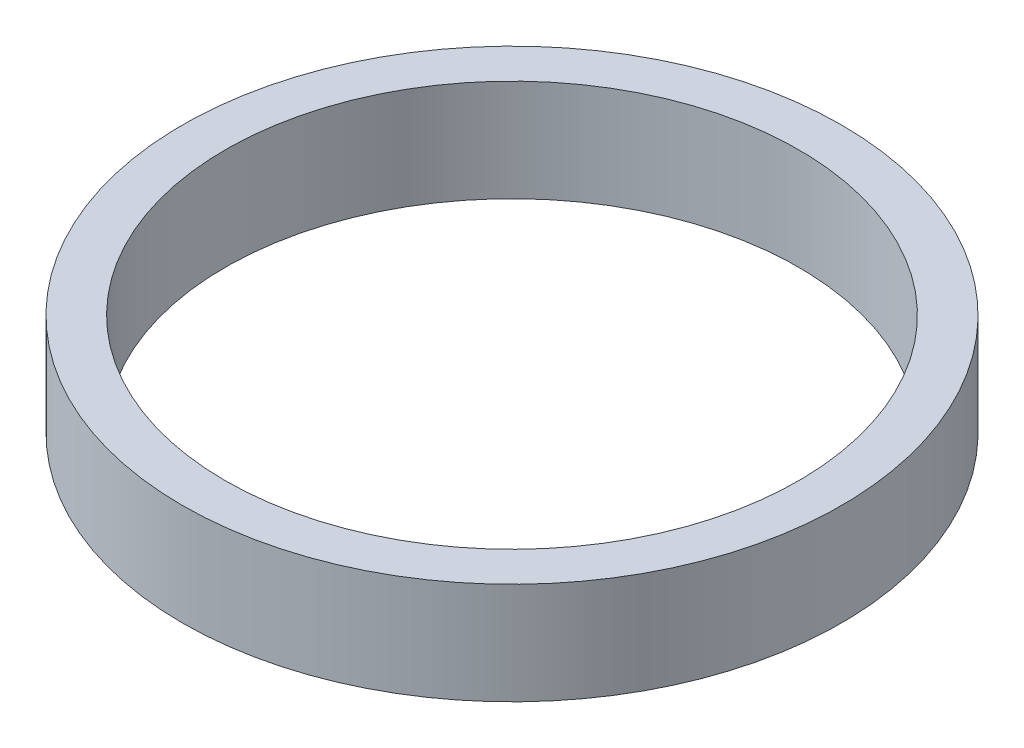
SolidWorks part; units mm, degrees
ref_plane "Front Plane" through (0, 0, 0) normal (0, 0, 1) x (1, 0, 0)
ref_plane "Top Plane" through (0, 0, 0) normal (0, 1, 0) x (1, 0, 0)
ref_plane "Right Plane" through (0, 0, 0) normal (1, 0, 0) x (0, 0, -1)
sketch "Sketch1" plane through (0, 0, 0) normal (0, 1, 0) x (1, 0, 0)
  circle A0 centre (0, 0) radius 53.5
  circle A1 centre (0, 0) radius 61.5
  dimension "D1" = 107
  dimension "D2" = 8
extrude "Boss-Extrude1" add sketch "Sketch1" along normal blind 19
